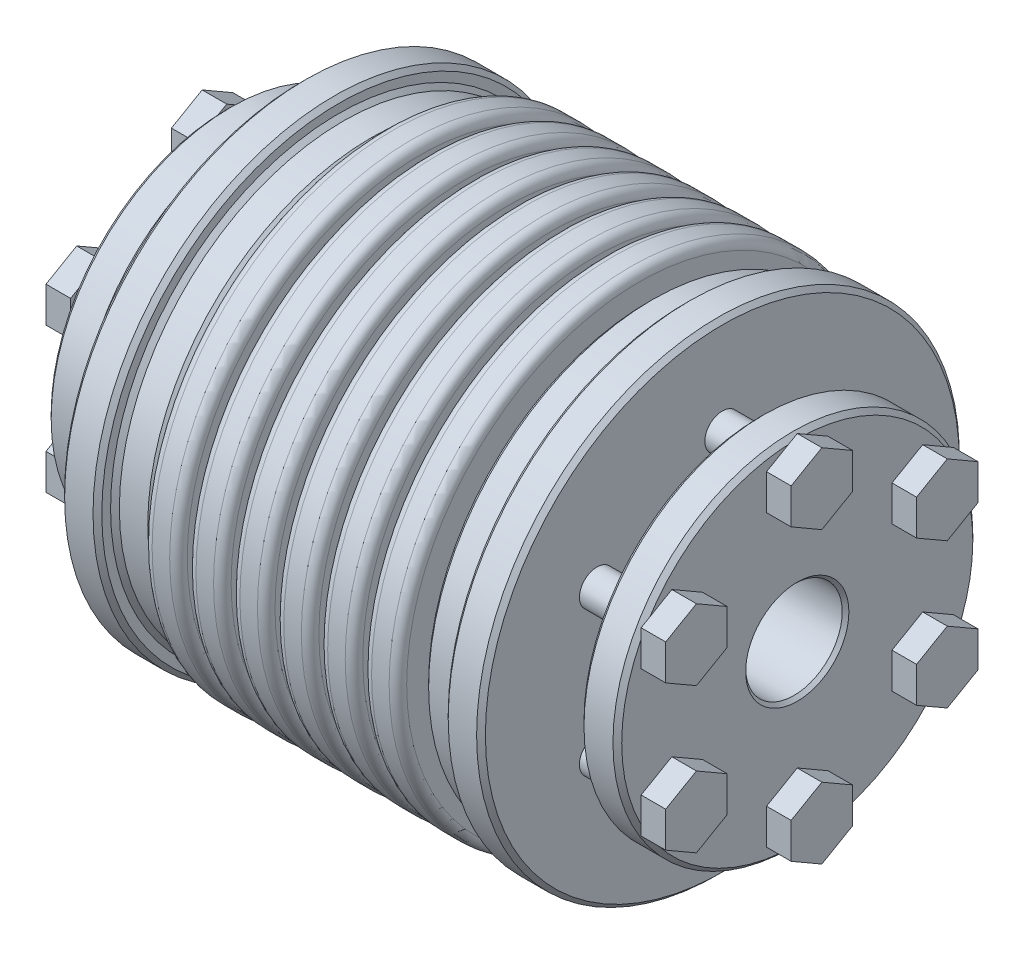
SolidWorks part; units mm, degrees
ref_plane "Front Plane" through (0, 0, 0) normal (0, 0, 1) x (1, 0, 0)
ref_plane "Top Plane" through (0, 0, 0) normal (0, 1, 0) x (1, 0, 0)
ref_plane "Right Plane" through (0, 0, 0) normal (1, 0, 0) x (0, 0, -1)
sketch "Sketch1" plane through (0, 0, 0) normal (1, 0, 0) x (0, 0, -1)
  circle A0 centre (0, 0) radius 27.5
  dimension "dim D" = 55
extrude "Boss-Extrude1" add sketch "Sketch1" along normal mid plane 65
sketch "Sketch2" plane through (32.5, 0, 0) normal (1, 0, 0) x (0, 0, -1)
  circle A0 centre (0, 0) radius 5.5
  dimension "dim d1" = 11
extrude "Cut-Extrude1" cut sketch "Sketch2" against normal blind 19
mirror "Mirror3" about plane through (0, 0, 0) normal (1, 0, 0) of "Cut-Extrude1"
chamfer "Chamfer1" distance 0.381 angle 45 4 edges at (-32.5, 0, -27.5) (32.5, 0, -27.5) (32.5, 0, -5.5) (-32.5, 0, -5.5)
ref_plane "L1" through (10.5, 0, 0) normal (1, 0, 0) x (0, 0, -1)
sketch "Sketch5" plane through (0, 0, 0) normal (1, 0, 0) x (0, 0, -1)
  line L0 (0, 5.881) -> (0, 27.5) construction
  circle A0 centre (0, 0) radius 5.881 construction
  circle A1 centre (0, 0) radius 16.6905
  circle A3 centre (0, 0) radius 27.5 construction
  point P9 (0, 16.6905)
extrude "Cut-Extrude2" cut sketch "Sketch5" against normal up to surface and the other way up to surface up to face at (-13.5, 0, -5.5) other way up to face at (13.5, 0, -5.5)
sketch "Sketch8" plane through (0, 0, 0) normal (0, 1, 0) x (1, 0, 0)
  line L0 (13.5, 16.6905) -> (-13.5, 16.6905) construction
  line L2 (-0.5, 18.6905) -> (0.5, 18.6905)
  line L3 (-0.5, 18.6905) -> (-0.5, 27.5)
  line L4 (-0.5, 27.5) -> (0.5, 27.5)
  line L5 (0, 18.6905) -> (0, 0) construction
  line L6 (0.5, 18.6905) -> (0.5, 27.5)
  line L7 (0, 0) -> (32.5, 0) construction
  line L8 (32.5, -27.119) -> (32.5, 27.119) construction
  line L9 (13.5, 5.5) -> (13.5, -5.5) construction
  line L10 (13.5, 5.5) -> (13.5, -5.5) construction
  line L11 (-32.5, -18.6905) -> (32.5, -18.6905) construction
  line L13 (0.5, 18.6905) -> (1.27, 18.6905) construction
  line L14 (-32.5, 27.119) -> (-32.5, -27.119) construction
  line L15 (4.5, 18.6905) -> (5.5, 18.6905)
  line L16 (4.5, 18.6905) -> (4.5, 27.5)
  line L17 (4.5, 27.5) -> (5.5, 27.5)
  line L18 (5.5, 18.6905) -> (5.5, 27.5)
  line L19 (9.5, 18.6905) -> (10.5, 18.6905)
  line L20 (9.5, 18.6905) -> (9.5, 27.5)
  line L21 (9.5, 27.5) -> (10.5, 27.5)
  line L22 (10.5, 18.6905) -> (10.5, 27.5)
  line L23 (14.5, 18.6905) -> (15.5, 18.6905)
  line L24 (14.5, 18.6905) -> (14.5, 27.5)
  line L25 (14.5, 27.5) -> (15.5, 27.5)
  line L26 (15.5, 18.6905) -> (15.5, 27.5)
  line L27 (-0.5, 18.6905) -> (4.5, 18.6905) construction
  line L28 (0, 0) -> (0, -18.6905) construction
  dimension "D2" = 4
  dimension "D1" = 1
  dimension "D3" = 2
  dimension "Dim L2" = 31
revolve "Cut-Revolve1" cut sketch "Sketch8" angle 360 about L7
mirror "Mirror2" about plane through (0, 0, 0) normal (1, 0, 0) of "Cut-Revolve1"
fillet "Fillet1" radius 1 14 edges at (0.5, 0, 27.5) (-0.5, 0, 27.5) (15.5, 0, 27.5) (14.5, 0, 27.5) (10.5, 0, 27.5) (9.5, 0, 27.5) (5.5, 0, 27.5) (4.5, 0, 27.5) (-14.5, 0, 27.5) (-10.5, 0, 27.5) (-9.5, 0, 27.5) (-5.5, 0, 27.5) (-4.5, 0, 27.5) (-15.5, 0, 27.5)
fillet "Fillet2" radius 0.25 14 edges at (-9.5, 0, 18.6905) (-4.5, 0, 18.6905) (0.5, 0, 18.6905) (5.5, 0, 18.6905) (10.5, 0, 18.6905) (15.5, 0, 18.6905) (14.5, 0, 18.6905) (9.5, 0, 18.6905) (4.5, 0, 18.6905) (-0.5, 0, 18.6905) (-5.5, 0, 18.6905) (-10.5, 0, 18.6905) (-14.5, 0, 18.6905) (-15.5, 0, 18.6905)
sketch "Sketch9" plane through (0, 0, 0) normal (0, 0, 1) x (1, 0, 0)
  line L0 (15.5, 25.5) -> (19.7337, 25.5)
  line L1 (15.5, 26.5) -> (15.5, -26.5) construction
  line L2 (19.7337, 25.5) -> (19.7337, 27.5)
  line L3 (32.119, 27.5) -> (16.5, 27.5) construction
  line L4 (19.7337, 27.5) -> (23.9673, 27.5)
  line L5 (23.9673, 27.5) -> (23.9673, 11.7535)
  line L6 (23.9673, 11.7535) -> (28.201, 12.5)
  line L7 (28.201, 12.5) -> (28.201, 20.5)
  line L8 (28.201, 20.5) -> (32.5, 20.5)
  line L9 (32.5, -27.119) -> (32.5, 27.119) construction
  line L10 (32.5, 20.5) -> (32.5, 32.5)
  line L11 (32.5, 32.5) -> (15.5, 32.5)
  line L12 (15.5, 32.5) -> (15.5, 25.5)
  line L13 (28.201, 12.5) -> (23.9673, 12.5) construction
  line L14 (32.119, 5.5) -> (32.119, 27.5) construction
  line L15 (32.119, 16.5) -> (28.201, 16.5) construction
  line L16 (32.5, 0) -> (-32.5, 0) construction
  line L17 (-32.5, 27.119) -> (-32.5, -27.119) construction
  line L18 (0, 0) -> (0, -27.1776) construction
  line L19 (-32.119, 16.5) -> (-28.201, 16.5) construction
  line L20 (-32.119, 5.5) -> (-32.119, 27.5) construction
  line L21 (-28.201, 12.5) -> (-23.9673, 12.5) construction
  line L22 (-15.5, 32.5) -> (-15.5, 25.5)
  line L23 (-32.5, 32.5) -> (-15.5, 32.5)
  line L24 (-32.5, 20.5) -> (-32.5, 32.5)
  line L25 (-28.201, 20.5) -> (-32.5, 20.5)
  line L26 (-28.201, 12.5) -> (-28.201, 20.5)
  line L27 (-23.9673, 11.7535) -> (-28.201, 12.5)
  line L28 (-23.9673, 27.5) -> (-23.9673, 11.7535)
  line L29 (-19.7337, 27.5) -> (-23.9673, 27.5)
  line L30 (-19.7337, 25.5) -> (-19.7337, 27.5)
  line L31 (-15.5, 25.5) -> (-19.7337, 25.5)
  dimension "D1" = 5
  dimension "D2" = 2
  dimension "D3" = 4
  dimension "D4" = 4
  dimension "D5" = 10
revolve "Cut-Revolve2" cut sketch "Sketch9" angle 360 about L16
sketch "Sketch10" plane through (32.5, 0, 0) normal (1, 0, 0) x (0, 0, -1)
  line L0 (0, 12.5) -> (0, 20.5) construction
  line L1 (10.7894, 6.2293) -> (14.2894, 4.2085)
  line L2 (0, 12.4585) -> (3.5, 14.4793)
  line L3 (3.5, 14.4793) -> (3.5, 18.5207)
  line L4 (3.5, 18.5207) -> (0, 20.5415)
  line L5 (0, 20.5415) -> (-3.5, 18.5207)
  line L6 (-3.5, 18.5207) -> (-3.5, 14.4793)
  line L7 (-3.5, 14.4793) -> (0, 12.4585)
  line L8 (14.2894, 4.2085) -> (17.7894, 6.2293)
  line L9 (17.7894, 6.2293) -> (17.7894, 10.2707)
  line L10 (17.7894, 10.2707) -> (14.2894, 12.2915)
  line L11 (14.2894, 12.2915) -> (10.7894, 10.2707)
  line L12 (10.7894, 10.2707) -> (10.7894, 6.2293)
  line L13 (10.8253, 6.25) -> (17.7535, 10.25) construction
  line L14 (10.7894, -6.2293) -> (10.7894, -10.2707)
  line L15 (10.7894, -10.2707) -> (14.2894, -12.2915)
  line L16 (14.2894, -12.2915) -> (17.7894, -10.2707)
  line L17 (17.7894, -10.2707) -> (17.7894, -6.2293)
  line L18 (17.7894, -6.2293) -> (14.2894, -4.2085)
  line L19 (14.2894, -4.2085) -> (10.7894, -6.2293)
  line L20 (10.8253, -6.25) -> (17.7535, -10.25) construction
  line L21 (0, -12.4585) -> (-3.5, -14.4793)
  line L22 (-3.5, -14.4793) -> (-3.5, -18.5207)
  line L23 (-3.5, -18.5207) -> (0, -20.5415)
  line L24 (0, -20.5415) -> (3.5, -18.5207)
  line L25 (3.5, -18.5207) -> (3.5, -14.4793)
  line L26 (3.5, -14.4793) -> (0, -12.4585)
  line L27 (0, -12.5) -> (0, -20.5) construction
  line L28 (-10.7894, -6.2293) -> (-14.2894, -4.2085)
  line L29 (-14.2894, -4.2085) -> (-17.7894, -6.2293)
  line L30 (-17.7894, -6.2293) -> (-17.7894, -10.2707)
  line L31 (-17.7894, -10.2707) -> (-14.2894, -12.2915)
  line L32 (-14.2894, -12.2915) -> (-10.7894, -10.2707)
  line L33 (-10.7894, -10.2707) -> (-10.7894, -6.2293)
  line L34 (-10.8253, -6.25) -> (-17.7535, -10.25) construction
  line L35 (-10.7894, 6.2293) -> (-10.7894, 10.2707)
  line L36 (-10.7894, 10.2707) -> (-14.2894, 12.2915)
  line L37 (-14.2894, 12.2915) -> (-17.7894, 10.2707)
  line L38 (-17.7894, 10.2707) -> (-17.7894, 6.2293)
  line L39 (-17.7894, 6.2293) -> (-14.2894, 4.2085)
  line L40 (-14.2894, 4.2085) -> (-10.7894, 6.2293)
  line L41 (-10.8253, 6.25) -> (-17.7535, 10.25) construction
  circle A0 centre (0, 0) radius 16.5 construction
  circle A1 centre (0, 0) radius 12.5 construction
  circle A2 centre (0, 0) radius 12.5 construction
  circle A3 centre (0, 0) radius 20.5 construction
  circle A4 centre (0, 16.5) radius 3.5 construction
  circle A5 centre (14.2894, 8.25) radius 3.5 construction
  circle A6 centre (14.2894, -8.25) radius 3.5 construction
  circle A7 centre (0, -16.5) radius 3.5 construction
  circle A8 centre (-14.2894, -8.25) radius 3.5 construction
  circle A9 centre (-14.2894, 8.25) radius 3.5 construction
  point P10 (0, 16.5)
  point P24 (14.2894, 8.25)
  point P35 (14.2894, -8.25)
  point P46 (0, -16.5)
  point P57 (-14.2894, -8.25)
  point P68 (-14.2894, 8.25)
  dimension "D1" = 6
  dimension "Dim Hex Head Width" = 7
extrude "Boss-Extrude2" add sketch "Sketch10" along normal blind 2.8 separate body
sketch "Sketch11" plane through (35.3, 0, 0) normal (1, 0, 0) x (0, 0, -1)
  line L0 (0, 20.5415) -> (0, 12.4585) construction
  line L1 (10.7894, 6.2293) -> (17.7894, 10.2707) construction
  circle A0 centre (0, 16.5) radius 2
  circle A1 centre (14.2894, 8.25) radius 2
  circle A2 centre (14.2894, -8.25) radius 2
  circle A3 centre (0, -16.5) radius 2
  circle A4 centre (-14.2894, -8.25) radius 2
  circle A5 centre (-14.2894, 8.25) radius 2
  dimension "D1" = 6
  dimension "Dim M" = 4
extrude "Boss-Extrude3" add sketch "Sketch11" against normal up to surface (11.3327 mm away) up to face at (23.9673, 0, -11.7535)
mirror "Mirror5" about plane through (0, 0, 0) normal (1, 0, 0) of bodies 123 124 125 126 127 128
chamfer "Chamfer2" distance 0.5 angle 45 12 edges at (28.201, 0, -20.5) (32.5, 0, -20.5) (23.9673, 0, -27.5) (19.7337, 0, -27.5) (15.5, 0, -25.5) (19.7337, 0, -25.5) (-32.5, 0, -20.5) (-28.201, 0, -20.5) (-23.9673, 0, -27.5) (-19.7337, 0, -27.5) (-19.7337, 0, -25.5) (-15.5, 0, -25.5)
